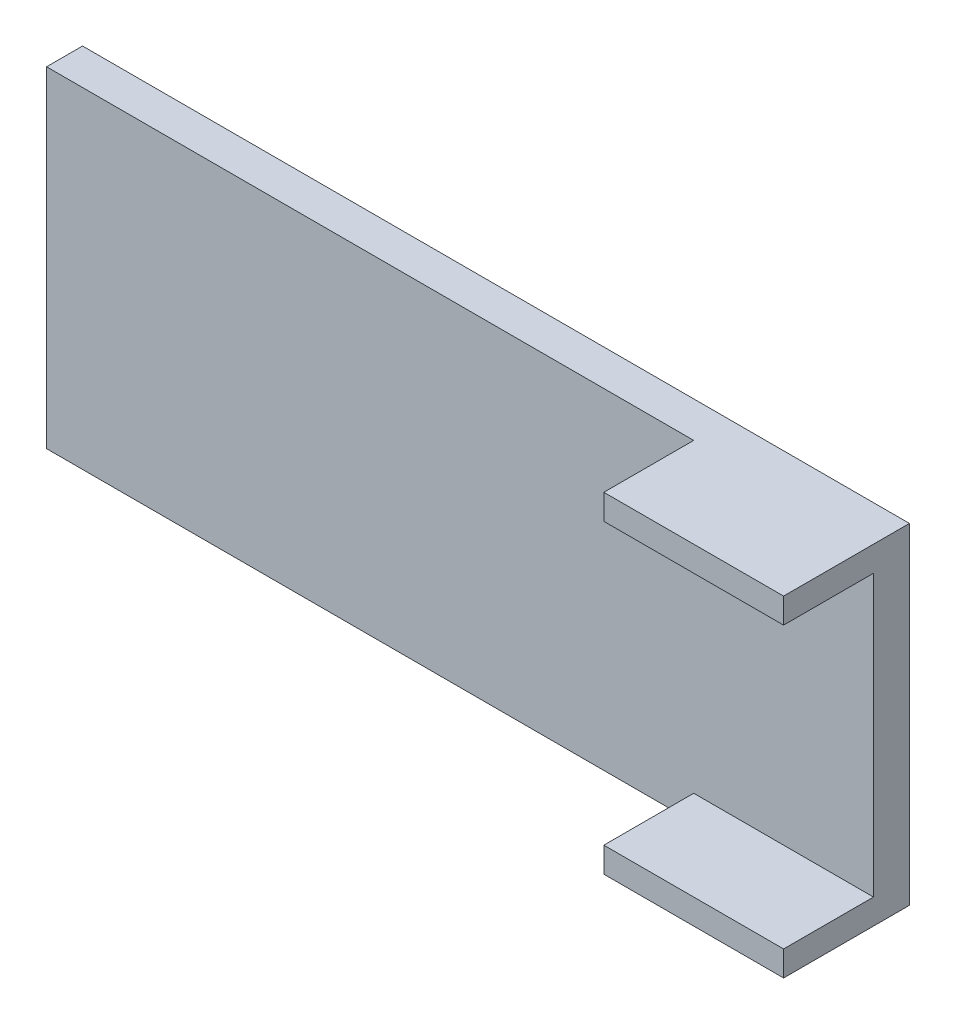
SolidWorks part; units mm, degrees
material "PPE"
ref_plane "Front Plane" through (0, 0, 0) normal (0, 0, 1) x (1, 0, 0)
ref_plane "Top Plane" through (0, 0, 0) normal (0, 1, 0) x (1, 0, 0)
ref_plane "Right Plane" through (0, 0, 0) normal (1, 0, 0) x (0, 0, -1)
sketch "Sketch2" plane through (0, 0, 0) normal (0, 0, 1) x (1, 0, 0)
  line L1 (-29.21, -11.684) -> (29.21, -11.684)
  line L2 (-29.21, -11.684) -> (-29.21, 11.684)
  line L3 (-29.21, 11.684) -> (29.21, 11.684)
  line L4 (29.21, -11.684) -> (29.21, 11.684)
  line L5 (-29.21, -11.684) -> (29.21, 11.684) construction
  line L6 (-29.21, 11.684) -> (29.21, -11.684) construction
  point P0 (0, 0)
  dimension "D1" = 58.42
  dimension "D2" = 23.368
extrude "Boss-Extrude1" add sketch "Sketch2" along normal blind 2.54
sketch "Sketch3" plane through (0, 0, 2.54) normal (0, 0, 1) x (1, 0, 0)
  line L0 (29.21, -11.684) -> (29.21, 11.684) construction
  line L3 (16.51, 9.906) -> (16.51, -9.906) construction
  line L4 (29.21, 11.684) -> (16.51, 11.684)
  line L5 (29.21, 11.684) -> (29.21, 9.906)
  line L6 (29.21, 9.906) -> (16.51, 9.906)
  line L7 (16.51, 11.684) -> (16.51, 9.906)
  line L8 (29.21, -11.684) -> (16.51, -11.684)
  line L9 (29.21, -11.684) -> (29.21, -9.906)
  line L10 (29.21, -9.906) -> (16.51, -9.906)
  line L11 (16.51, -11.684) -> (16.51, -9.906)
  dimension "D1" = 19.812
  dimension "D2" = 12.7
extrude "Boss-Extrude2" add sketch "Sketch3" along normal blind 6.35
scale "Scale1" [suppressed]
